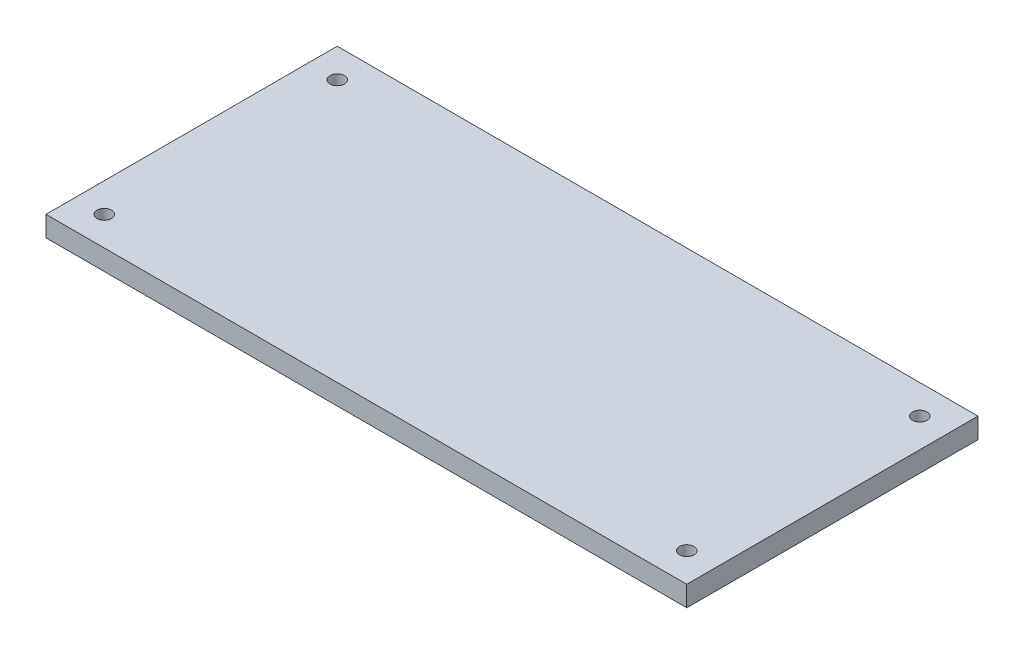
SolidWorks part; units mm, degrees
ref_plane "Front Plane" through (0, 0, 0) normal (0, 0, 1) x (1, 0, 0)
ref_plane "Top Plane" through (0, 0, 0) normal (0, 1, 0) x (1, 0, 0)
ref_plane "Right Plane" through (0, 0, 0) normal (1, 0, 0) x (0, 0, -1)
sketch "Sketch1" plane through (0, 0, 0) normal (0, 1, 0) x (1, 0, 0)
  line L1 (0, 0) -> (279.4, 0)
  line L2 (0, 0) -> (0, -127)
  line L3 (0, -127) -> (279.4, -127)
  line L4 (279.4, 0) -> (279.4, -127)
  circle A0 centre (12.7, -12.7) radius 3.175
  circle A1 centre (12.7, -114.3) radius 3.175
  circle A2 centre (266.7, -12.7) radius 3.175
  circle A3 centre (266.7, -114.3) radius 3.175
  dimension "D3" = 6.35
  dimension "D4" = 6.35
  dimension "D5" = 6.35
  dimension "D6" = 6.35
  dimension "D1" = 127
  dimension "D2" = 279.4
  dimension "D7" = 12.7
  dimension "D8" = 12.7
  dimension "D9" = 12.7
  dimension "D10" = 12.7
  dimension "D11" = 12.7
  dimension "D12" = 12.7
  dimension "D13" = 12.7
  dimension "D14" = 12.7
extrude "Boss-Extrude1" add sketch "Sketch1" along normal blind 8.89
